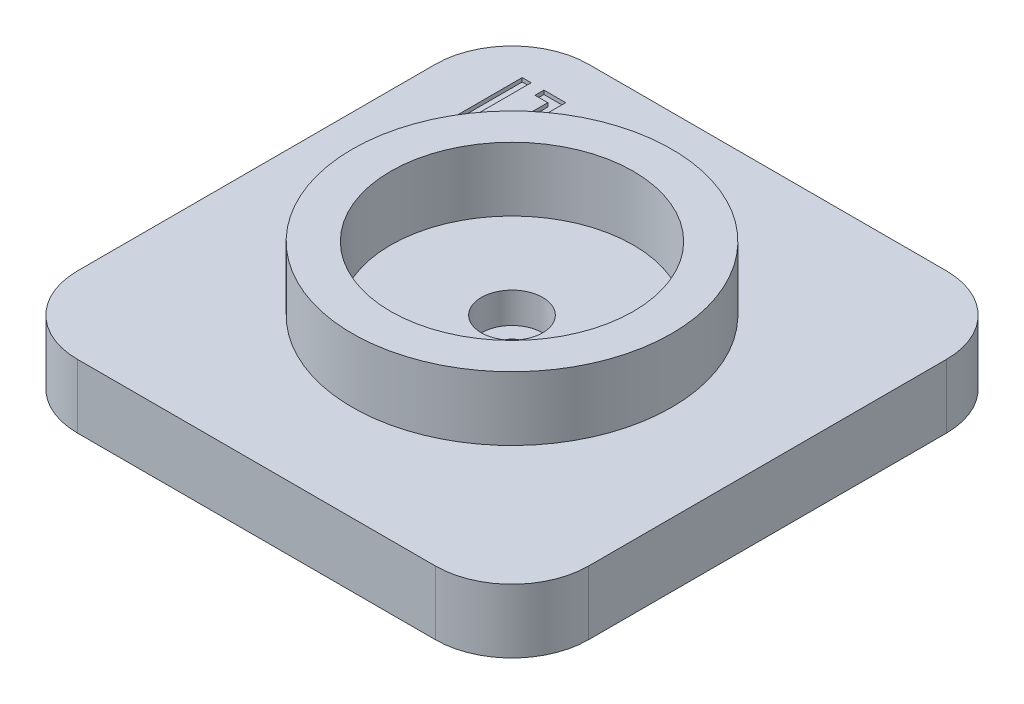
SolidWorks part; units mm, degrees
ref_plane "Alzado" through (0, 0, 0) normal (0, 0, 1) x (1, 0, 0)
ref_plane "Planta" through (0, 0, 0) normal (0, 1, 0) x (1, 0, 0)
ref_plane "Vista lateral" through (0, 0, 0) normal (1, 0, 0) x (0, 0, -1)
sketch "Croquis1" plane through (0, 0, 0) normal (0, 1, 0) x (1, 0, 0)
  line L1 (-14, 20) -> (14, 20)
  line L2 (-20, 14) -> (-20, -14)
  line L3 (-14, -20) -> (14, -20)
  line L4 (20, 14) -> (20, -14)
  line L5 (-20, 20) -> (20, -20) construction
  line L6 (-20, -20) -> (20, 20) construction
  arc A0 (-20, -14) -> (-14, -20) centre (-14, -14) ccw
  arc A1 (-14, 20) -> (-20, 14) centre (-14, 14) ccw
  arc A2 (14, 20) -> (20, 14) centre (14, 14) cw
  arc A3 (14, -20) -> (20, -14) centre (14, -14) ccw
  point P0 (0, 0)
  dimension "D3" = 6
  dimension "D1" = 40
  dimension "D2" = 40
extrude "Saliente-Extruir1" add sketch "Croquis1" along normal blind 4 and the other way blind 1
sketch "Croquis4" plane through (0, -1, 0) normal (0, -1, 0) x (1, 0, 0)
  circle A0 centre (0, 0) radius 6
  dimension "D1" = 12
extrude "Cortar-Extruir1" cut sketch "Croquis4" against normal blind 1.5
sketch "Croquis8" plane through (0, 4, 0) normal (0, 1, 0) x (1, 0, 0)
  circle A0 centre (0, 0) radius 2.4
  dimension "D1" = 4.8
extrude "Cortar-Extruir2" cut sketch "Croquis8" against normal blind 2.4
sketch "Croquis9" plane through (0, 1.6, 0) normal (0, 1, 0) x (1, 0, 0)
  circle A0 centre (0, 0) radius 1.1
  dimension "D1" = 2.2
extrude "Cortar-Extruir3" cut sketch "Croquis9" against normal up to next
sketch "Croquis10" plane through (0, 4, 0) normal (0, 1, 0) x (1, 0, 0)
  circle A0 centre (0, 0) radius 9.5
  dimension "D1" = 19
extrude "Extruir-Lámina1" add sketch "Croquis10" along normal blind 5 thin
sketch "Croquis11" plane through (0, 4, 0) normal (0, 1, 0) x (1, 0, 0)
  line L0 (-14, 17) -> (-14, 11) construction
  line L1 (-18.1835, 14) -> (-9.8165, 14) construction
  line L2 (-14, 11.5) -> (-14, 12.2)
  line L3 (-14, 12.2) -> (-15, 12.2)
  line L4 (-15, 12.2) -> (-15, 16.5)
  line L5 (-15, 16.5) -> (-15.7, 16.5)
  line L6 (-15.7, 16.5) -> (-15.7, 11.5)
  line L7 (-15.7, 11.5) -> (-14, 11.5)
  line L9 (-12.3, 16.5) -> (-14, 16.5)
  line L10 (-14, 16.5) -> (-14, 15.8)
  line L11 (-14, 15.8) -> (-13, 15.8)
  line L12 (-13, 15.8) -> (-13, 11.5)
  line L13 (-13, 11.5) -> (-12.3, 11.5)
  line L14 (-12.3, 11.5) -> (-12.3, 16.5)
  point P4 (-15.7, 14)
  point P16 (-14, 14)
  point P17 (-12.3, 14)
  point P23 (-14, 14)
  dimension "D1" = 6
  dimension "D2" = 0.7
  dimension "D3" = 5
  dimension "D4" = 0.7
  dimension "D5" = 1
  dimension "D6" = 0
  dimension "D7" = 0
  dimension "D8" = 2
extrude "Cortar-Extruir4" cut sketch "Croquis11" against normal blind 0.3
